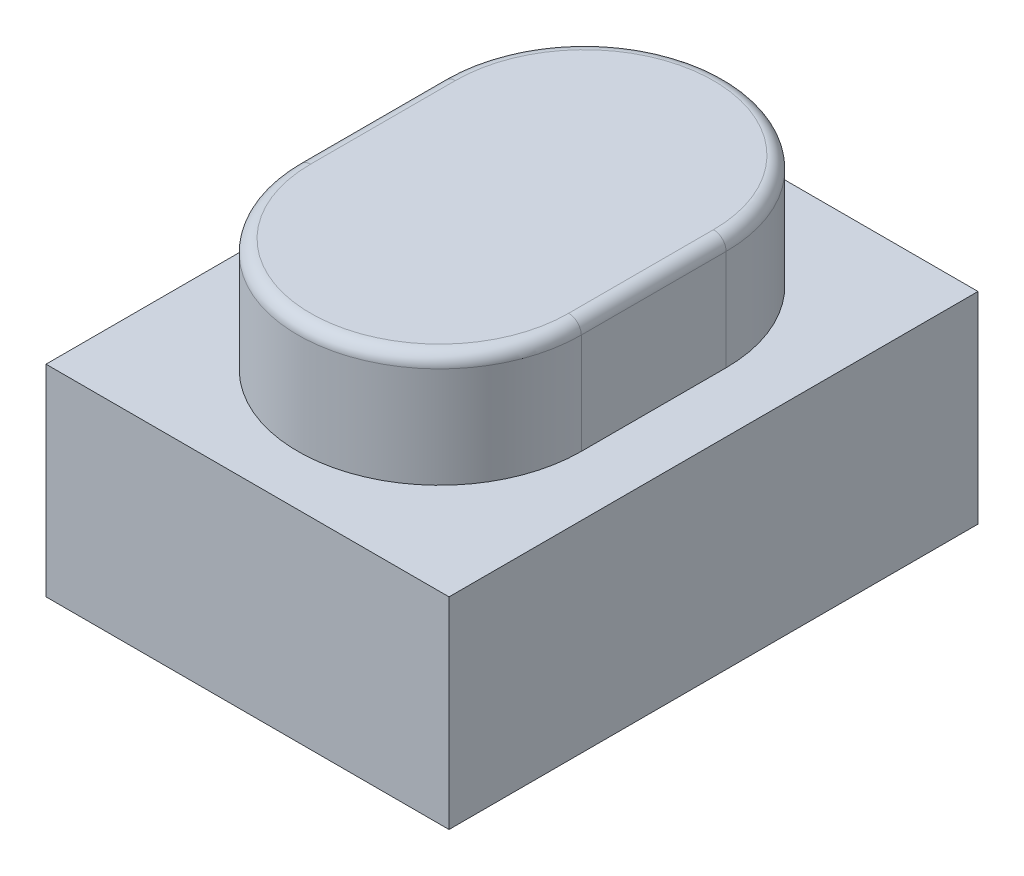
SolidWorks part; units mm, degrees
ref_plane "Front Plane" through (0, 0, 0) normal (0, 0, 1) x (1, 0, 0)
ref_plane "Top Plane" through (0, 0, 0) normal (0, 1, 0) x (1, 0, 0)
ref_plane "Right Plane" through (0, 0, 0) normal (1, 0, 0) x (0, 0, -1)
sketch "BaseS" plane through (0, 0, 0) normal (0, 1, 0) x (1, 0, 0)
  line L1 (-1.6, 2.1) -> (1.6, 2.1)
  line L2 (-1.6, 2.1) -> (-1.6, -2.1)
  line L3 (-1.6, -2.1) -> (1.6, -2.1)
  line L4 (1.6, 2.1) -> (1.6, -2.1)
  line L5 (-1.6, 2.1) -> (1.6, -2.1) construction
  line L6 (-1.6, -2.1) -> (1.6, 2.1) construction
  point P0 (0, 0)
  dimension "Width" = 3.2
  dimension "Length" = 4.2
extrude "Base" add sketch "BaseS" along normal blind 1.6
sketch "ButtonS" plane through (0, 1.6, 0) normal (0, 1, 0) x (1, 0, 0)
  line L0 (0, 0.575) -> (0, -0.575) construction
  line L1 (1.125, 0.575) -> (1.125, -0.575)
  line L2 (-1.125, 0.575) -> (-1.125, -0.575)
  arc A0 (1.125, 0.575) -> (-1.125, 0.575) centre (0, 0.575) ccw
  arc A1 (-1.125, -0.575) -> (1.125, -0.575) centre (0, -0.575) ccw
  point P2 (0, 0)
  dimension "Width" = 2.25
  dimension "Height" = 1.15
extrude "Button" add sketch "ButtonS" along normal blind 0.9
fillet "BF" radius 0.1 4 edges at (1.125, 2.5, 0) (0, 2.5, 1.7) (-1.125, 2.5, 0) (0, 2.5, -1.7)
